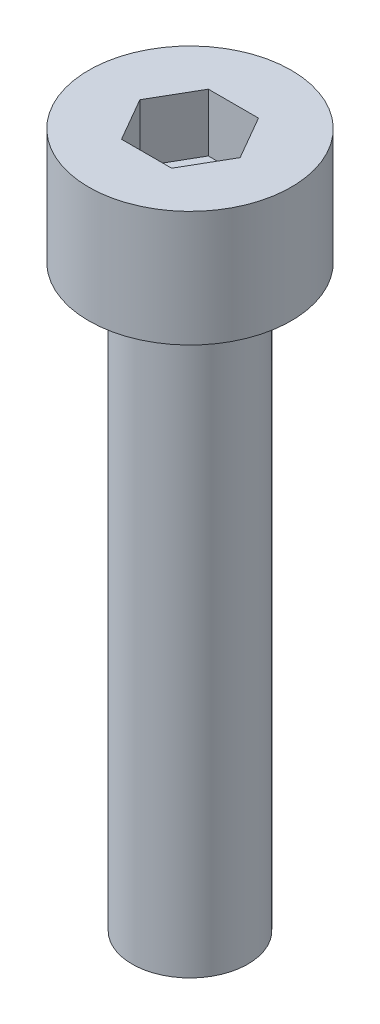
SolidWorks part; units mm, degrees
material "AISI 304"
ref_plane "前视基准面" through (0, 0, 0) normal (0, 0, 1) x (1, 0, 0)
ref_plane "上视基准面" through (0, 0, 0) normal (0, 1, 0) x (1, 0, 0)
ref_plane "右视基准面" through (0, 0, 0) normal (1, 0, 0) x (0, 0, -1)
sketch "草图1" plane through (0, 0, 0) normal (0, 1, 0) x (1, 0, 0)
  circle A0 centre (0, 0) radius 3.5
  dimension "D1" = 7
extrude "杯头" add sketch "草图1" along normal blind 4
sketch "草图2" plane through (0, 4, 0) normal (0, 1, 0) x (1, 0, 0)
  line L1 (1.7321, 0) -> (0.866, 1.5)
  line L2 (0.866, 1.5) -> (-0.866, 1.5)
  line L3 (-0.866, 1.5) -> (-1.7321, 0)
  line L4 (-1.7321, 0) -> (-0.866, -1.5)
  line L5 (-0.866, -1.5) -> (0.866, -1.5)
  line L6 (0.866, -1.5) -> (1.7321, 0)
  circle A0 centre (0, 0) radius 1.5 construction
  dimension "D1" = 3
extrude "内六角口" cut sketch "草图2" against normal blind 2
sketch "草图3" plane through (0, 0, 0) normal (0, -1, 0) x (1, 0, 0)
  circle A0 centre (0, 0) radius 2
  dimension "D1" = 4
extrude "螺纹长度" add sketch "草图3" along normal blind 20
